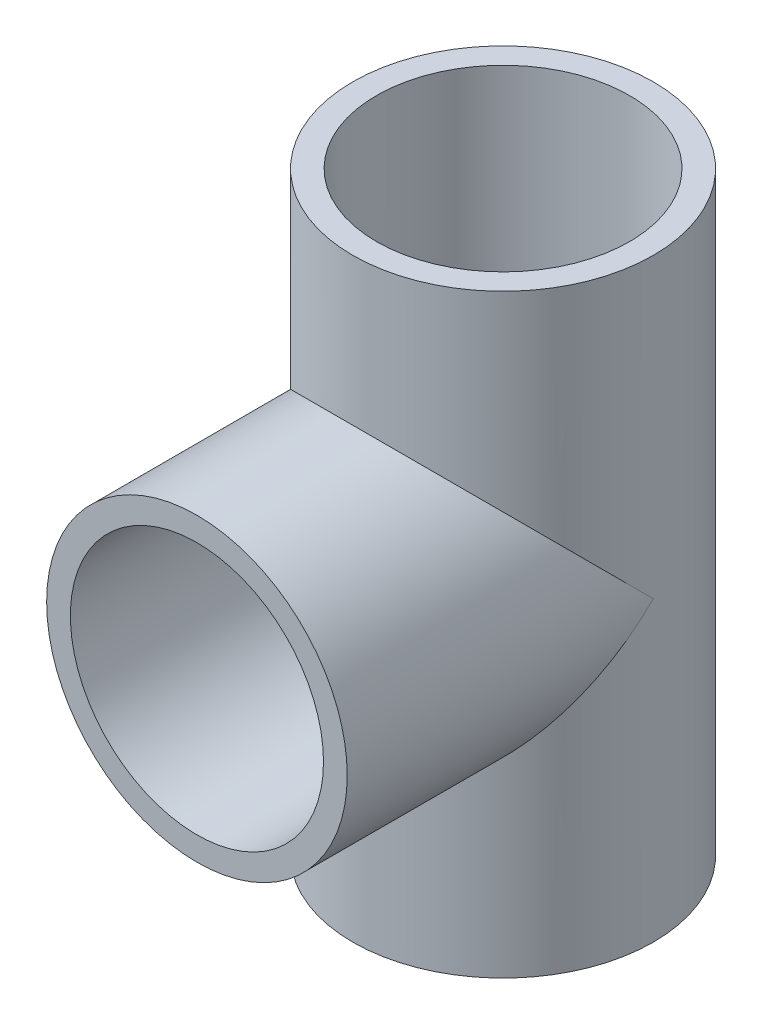
SolidWorks part; units mm, degrees
ref_plane "前视基准面" through (0, 0, 0) normal (0, 0, 1) x (1, 0, 0)
ref_plane "上视基准面" through (0, 0, 0) normal (0, 1, 0) x (1, 0, 0)
ref_plane "右视基准面" through (0, 0, 0) normal (1, 0, 0) x (0, 0, -1)
sketch "草图1" plane through (0, 0, 0) normal (0, 1, 0) x (1, 0, 0)
  circle A0 centre (0, 0) radius 16
  circle A1 centre (0, 0) radius 19
  dimension "D1" = 32
  dimension "D2" = 38
extrude "凸台-拉伸1" add sketch "草图1" along normal blind 75.2 contours A1 | A0
sketch "草图2" plane through (0, 0, 0) normal (0, 0, 1) x (1, 0, 0)
  line L0 (0, 75.2) -> (0, 0) construction
  line L1 (19, 75.2) -> (-19, 75.2) construction
  line L2 (-19, 0) -> (19, 0) construction
  circle A0 centre (0, 37.6) radius 16
  circle A1 centre (0, 37.6) radius 19
extrude "凸台-拉伸2" add sketch "草图2" along normal blind 38.7 contours A1 | A0
sketch "草图3" plane through (0, 75.2, 0) normal (0, 1, 0) x (1, 0, 0)
  circle A0 centre (0, 0) radius 16
extrude "切除-拉伸1" cut sketch "草图3" against normal through all
sketch "草图4" plane through (0, 0, 38.7) normal (0, 0, 1) x (1, 0, 0)
  circle A2 centre (0, 37.6) radius 16
extrude "切除-拉伸2" cut sketch "草图4" against normal up to next
